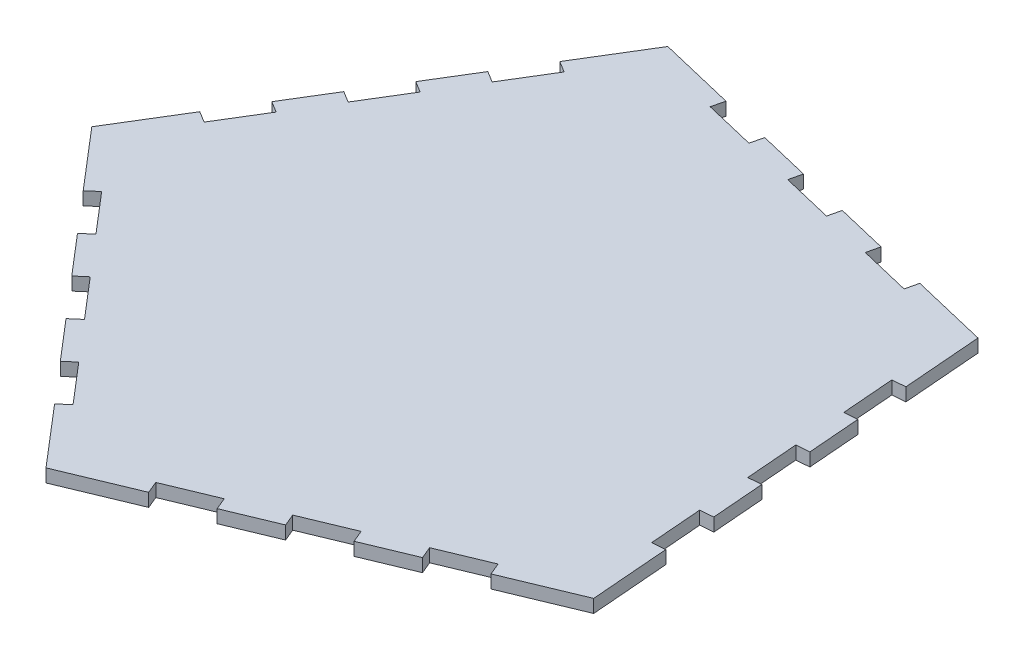
SolidWorks part; units mm, degrees
ref_plane "Front Plane" through (0, 0, 0) normal (0, 0, 1) x (1, 0, 0)
ref_plane "Top Plane" through (0, 0, 0) normal (0, 1, 0) x (1, 0, 0)
ref_plane "Right Plane" through (0, 0, 0) normal (1, 0, 0) x (0, 0, -1)
sketch "Sketch1" plane through (0, 0, 0) normal (0, 1, 0) x (1, 0, 0)
  line L1 (67.038, -56.8839) -> (50.8579, 145.6709)
  line L2 (50.8579, 145.6709) -> (-146.7831, 192.8756)
  line L3 (-146.7831, 192.8756) -> (-252.7518, 19.4949)
  line L4 (-252.7518, 19.4949) -> (-120.6031, -134.865)
  line L5 (-120.6031, -134.865) -> (67.038, -56.8839)
  circle A0 centre (-80.4484, 33.2585) radius 139.8404 construction
  dimension "D1" = 203.2
extrude "Boss-Extrude1" add sketch "Sketch1" along normal blind 6.35
sketch "Sketch2" plane through (0, 6.35, 0) normal (0, 1, 0) x (1, 0, 0)
  line L0 (-120.6031, -134.865) -> (67.038, -56.8839) construction
  line L1 (-87.8573, -114.3797) -> (-64.4021, -104.6321)
  line L2 (-87.8573, -114.3797) -> (-85.4204, -120.2435)
  line L3 (-85.4204, -120.2435) -> (-61.9652, -110.4959)
  line L4 (-64.4021, -104.6321) -> (-61.9652, -110.4959)
  line L5 (-124.6806, -129.683) -> (66.5064, -50.2283) construction
  line L6 (-38.5101, -100.7482) -> (-15.055, -91.0006)
  line L7 (-38.5101, -100.7482) -> (-40.947, -94.8845)
  line L8 (-40.947, -94.8845) -> (-17.4919, -85.1368)
  line L9 (-15.055, -91.0006) -> (-17.4919, -85.1368)
  line L10 (8.4002, -81.253) -> (31.8553, -71.5053)
  line L11 (8.4002, -81.253) -> (5.9633, -75.3892)
  line L12 (5.9633, -75.3892) -> (29.4184, -65.6416)
  line L13 (31.8553, -71.5053) -> (29.4184, -65.6416)
  line L14 (67.038, -56.8839) -> (50.8579, 145.6709) construction
  line L15 (-146.7831, 192.8756) -> (-26.7825, -95.8744) construction
  line L16 (-223.1502, -5.318) -> (-206.6316, -24.6129)
  line L17 (50.8579, 145.6709) -> (-186.6774, -57.6851) construction
  line L18 (-252.7518, 19.4949) -> (-120.6031, -134.865) construction
  line L19 (-227.9739, -9.4476) -> (-211.4553, -28.7426)
  line L20 (-146.7831, 192.8756) -> (-252.7518, 19.4949) construction
  line L21 (-199.7674, 106.1852) -> (67.038, -56.8839) construction
  line L22 (-223.1502, -5.318) -> (-227.9739, -9.4476)
  line L23 (-206.6316, -24.6129) -> (-211.4553, -28.7426)
  line L24 (-194.9367, -48.0376) -> (-190.113, -43.9079)
  line L25 (-190.113, -43.9079) -> (-173.5944, -63.2029)
  line L26 (-194.9367, -48.0376) -> (-178.4182, -67.3325)
  line L27 (-178.4182, -67.3325) -> (-173.5944, -63.2029)
  line L28 (-161.8996, -86.6275) -> (-157.0758, -82.4979)
  line L29 (-157.0758, -82.4979) -> (-140.5572, -101.7929)
  line L30 (-145.381, -105.9225) -> (-140.5572, -101.7929)
  line L31 (-161.8996, -86.6275) -> (-145.381, -105.9225)
  line L32 (-161.2341, 157.0552) -> (-174.4802, 135.3826)
  line L33 (-166.6522, 160.3667) -> (-179.8983, 138.6941)
  line L34 (-161.2341, 157.0552) -> (-166.6522, 160.3667)
  line L35 (-174.4802, 135.3826) -> (-179.8983, 138.6941)
  line L36 (-193.1444, 117.0215) -> (-187.7262, 113.71)
  line L37 (-187.7262, 113.71) -> (-200.9723, 92.0374)
  line L38 (-193.1444, 117.0215) -> (-206.3905, 95.3489)
  line L39 (-206.3905, 95.3489) -> (-200.9723, 92.0374)
  line L40 (-219.6366, 73.6763) -> (-214.2184, 70.3648)
  line L41 (-214.2184, 70.3648) -> (-227.4645, 48.6922)
  line L42 (-232.8827, 52.0037) -> (-227.4645, 48.6922)
  line L43 (-219.6366, 73.6763) -> (-232.8827, 52.0037)
  line L44 (12.3251, 148.3455) -> (-12.38, 154.2461)
  line L45 (13.8002, 154.5218) -> (-10.9049, 160.4224)
  line L46 (12.3251, 148.3455) -> (13.8002, 154.5218)
  line L47 (-12.38, 154.2461) -> (-10.9049, 160.4224)
  line L48 (-35.61, 166.3229) -> (-37.0852, 160.1467)
  line L49 (-37.0852, 160.1467) -> (-61.7903, 166.0472)
  line L50 (-35.61, 166.3229) -> (-60.3151, 172.2235)
  line L51 (-60.3151, 172.2235) -> (-61.7903, 166.0472)
  line L52 (-85.0203, 178.1241) -> (-86.4954, 171.9478)
  line L53 (-86.4954, 171.9478) -> (-111.2005, 177.8484)
  line L54 (-109.7254, 184.0247) -> (-111.2005, 177.8484)
  line L55 (-85.0203, 178.1241) -> (-109.7254, 184.0247)
  line L56 (57.6744, -19.4105) -> (55.6519, 5.9089)
  line L57 (64.0043, -18.9049) -> (61.9817, 6.4145)
  line L58 (57.6744, -19.4105) -> (64.0043, -18.9049)
  line L59 (55.6519, 5.9089) -> (61.9817, 6.4145)
  line L60 (59.9592, 31.7338) -> (53.6294, 31.2282)
  line L61 (53.6294, 31.2282) -> (51.6069, 56.5476)
  line L62 (59.9592, 31.7338) -> (57.9367, 57.0532)
  line L63 (57.9367, 57.0532) -> (51.6069, 56.5476)
  line L64 (55.9142, 82.3725) -> (49.5844, 81.8669)
  line L65 (49.5844, 81.8669) -> (47.5618, 107.1863)
  line L66 (53.8917, 107.6919) -> (47.5618, 107.1863)
  line L67 (55.9142, 82.3725) -> (53.8917, 107.6919)
  point P27 (-80.4484, 33.2585)
  point P84 (-80.4484, 33.2585)
  dimension "D1" = 38.1
  dimension "D2" = 25.4
  dimension "D3" = 6.35
  dimension "D4" = 25.4
  dimension "D5" = 25.4
  dimension "D6" = 6.35
  dimension "D7" = 25.4
  dimension "D8" = 25.4
  dimension "D9" = 6.35
  dimension "D10" = 5
extrude "Cut-Extrude1" cut sketch "Sketch2" against normal through all
